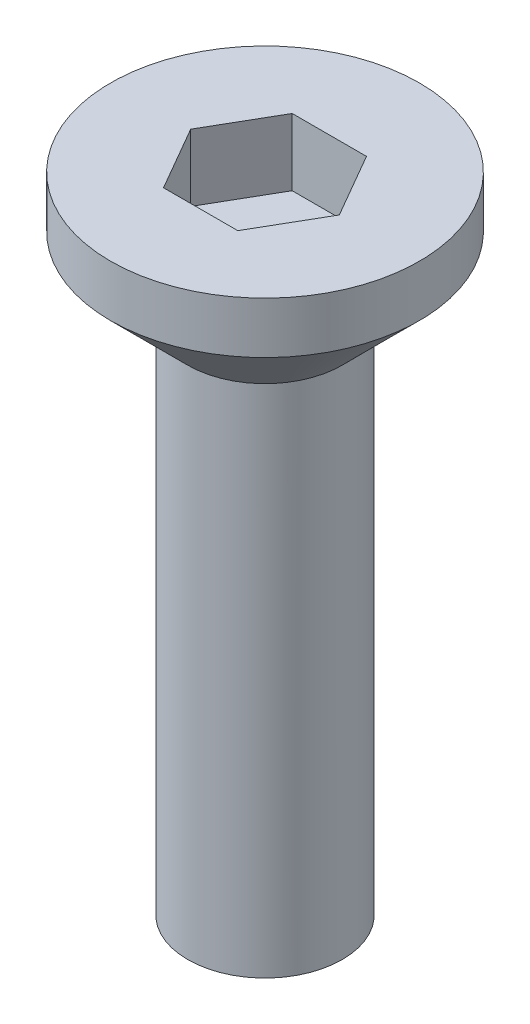
SolidWorks part; units mm, degrees
material "AISI 304"
ref_plane "前视基准面" through (0, 0, 0) normal (0, 0, 1) x (1, 0, 0)
ref_plane "上视基准面" through (0, 0, 0) normal (0, 1, 0) x (1, 0, 0)
ref_plane "右视基准面" through (0, 0, 0) normal (1, 0, 0) x (0, 0, -1)
sketch "草图1" plane through (0, 0, 0) normal (0, 1, 0) x (1, 0, 0)
  circle A0 centre (0, 0) radius 3
  dimension "D1" = 6
extrude "沉头头" add sketch "草图1" along normal blind 2.5
chamfer "倒角1" distance 1.5 angle 45 1 edges at (0, 0, 3)
sketch "草图2" plane through (0, 2.5, 0) normal (0, 1, 0) x (1, 0, 0)
  line L1 (1.4434, 0) -> (0.7217, 1.25)
  line L2 (0.7217, 1.25) -> (-0.7217, 1.25)
  line L3 (-0.7217, 1.25) -> (-1.4434, 0)
  line L4 (-1.4434, 0) -> (-0.7217, -1.25)
  line L5 (-0.7217, -1.25) -> (0.7217, -1.25)
  line L6 (0.7217, -1.25) -> (1.4434, 0)
  circle A0 centre (0, 0) radius 1.25 construction
  dimension "D1" = 2.5
extrude "内六角口" cut sketch "草图2" against normal blind 1.3
sketch "草图3" plane through (0, 0, 0) normal (0, -1, 0) x (1, 0, 0)
  circle A0 centre (0, 0) radius 1.5
  dimension "D1" = 3
extrude "螺纹长" add sketch "草图3" along normal blind 10
